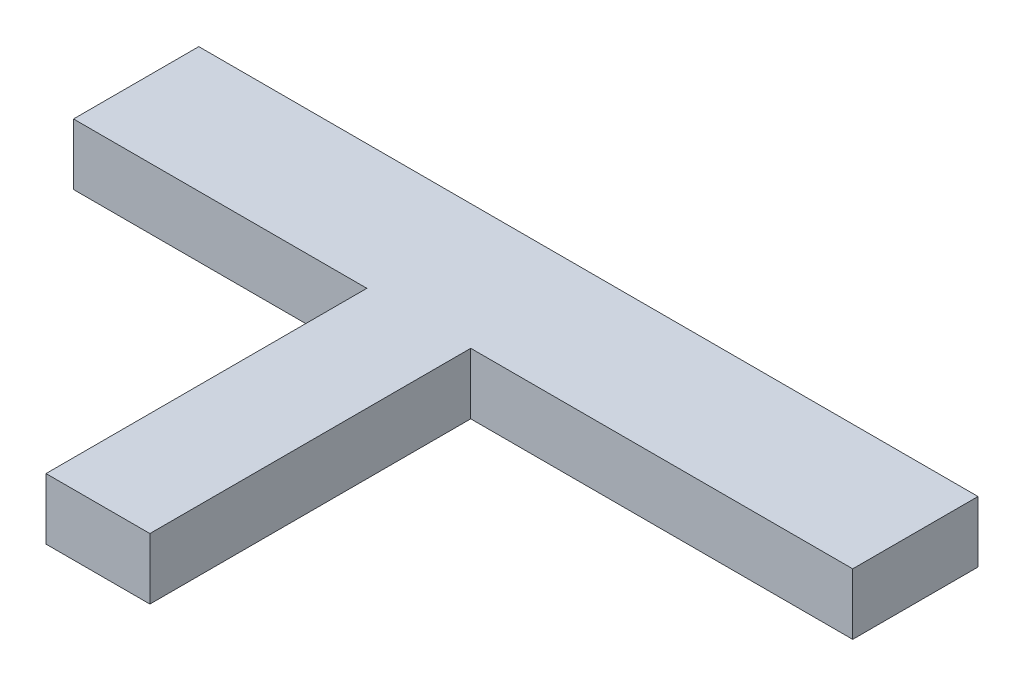
SolidWorks part; units mm, degrees
ref_plane "Front Plane" through (0, 0, 0) normal (0, 0, 1) x (1, 0, 0)
ref_plane "Top Plane" through (0, 0, 0) normal (0, 1, 0) x (1, 0, 0)
ref_plane "Right Plane" through (0, 0, 0) normal (1, 0, 0) x (0, 0, -1)
sketch "Sketch2" plane through (0, 0, 0) normal (0, 1, 0) x (1, 0, 0)
  line L1 (-153.8906, 76.3272) -> (169.9594, 76.3272)
  line L2 (-153.8906, 76.3272) -> (-153.8906, -109.0928)
  line L3 (-153.8906, -109.0928) -> (169.9594, -109.0928)
  line L4 (169.9594, 76.3272) -> (169.9594, -109.0928)
  dimension "D1" = 323.85
  dimension "D2" = 185.42
extrude "Boss-Extrude1" add sketch "Sketch2" along normal blind 25.4
sketch "Sketch3" plane through (0, 25.4, 0) normal (0, 1, 0) x (1, 0, 0)
  line L0 (-153.8906, 76.3272) -> (-153.8906, -109.0928) construction
  line L2 (-153.8906, -12.5061) -> (-153.8906, -109.0928)
  line L3 (-153.8906, -109.0928) -> (-20.5406, -109.0928)
  line L5 (-153.8906, -109.0928) -> (169.9594, -109.0928) construction
  line L6 (169.9594, -109.0928) -> (169.9594, 76.3272) construction
  line L7 (169.9594, 24.2572) -> (11.2094, 24.2572)
  line L8 (169.9594, 24.2572) -> (169.9594, -109.0928)
  line L9 (169.9594, -109.0928) -> (11.2094, -109.0928)
  line L10 (11.2094, 24.2572) -> (11.2094, -109.0928)
  line L12 (-153.8906, 24.2572) -> (-31.9706, 24.2572)
  line L13 (-153.8906, 24.2572) -> (-153.8906, -109.0928)
  line L14 (-153.8906, -109.0928) -> (-31.9706, -109.0928)
  line L15 (-31.9706, 24.2572) -> (-31.9706, -109.0928)
  line M8 (-153.8906, 76.3272) -> (-153.8906, -109.0928)
  line M9 (-153.8906, -109.0928) -> (169.9594, -109.0928)
  line M10 (169.9594, -109.0928) -> (169.9594, 76.3272)
  dimension "D1" = 158.75
  dimension "D2" = 133.35
  dimension "D3" = 43.18
extrude "Cut-Extrude2" cut sketch "Sketch3" against normal blind 25.4 contours L15 L12 M8 M9 | L7 L10 M9 M10
